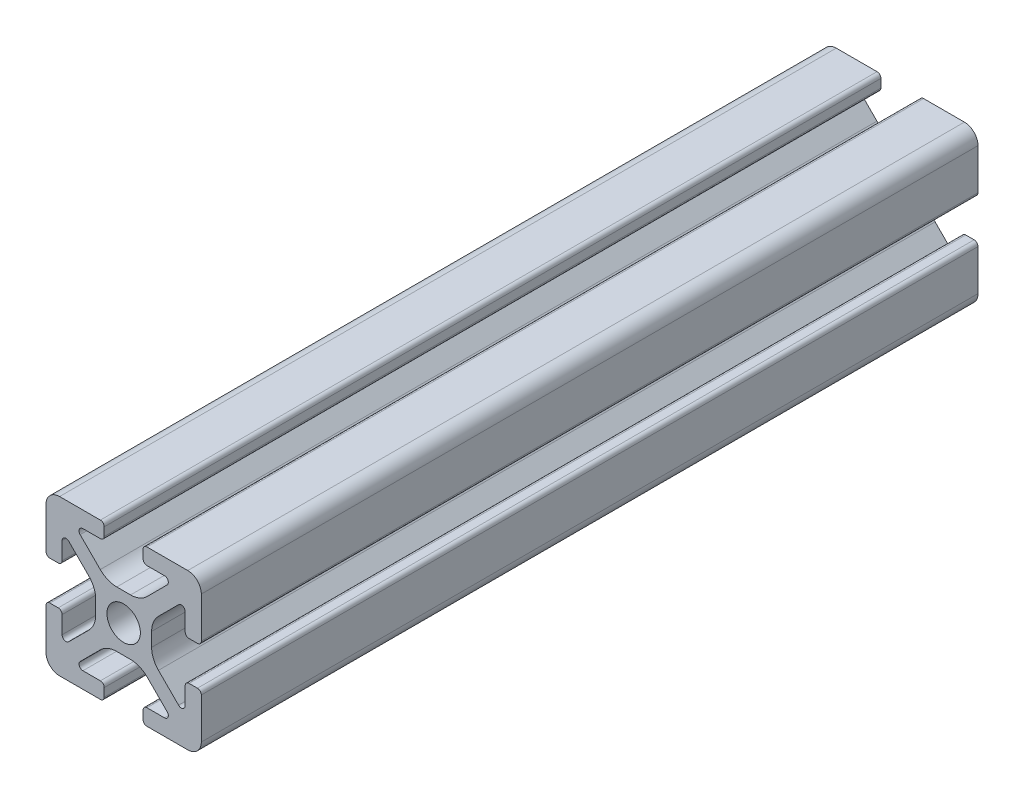
SolidWorks part; units mm, degrees
material "6061 Alloy"
ref_plane "Front Plane" through (0, 0, 0) normal (0, 0, 1) x (1, 0, 0)
ref_plane "Top Plane" through (0, 0, 0) normal (0, 1, 0) x (1, 0, 0)
ref_plane "Right Plane" through (0, 0, 0) normal (1, 0, 0) x (0, 0, -1)
sketch "Sketch2" plane through (0, 0, 0) normal (0, 0, 1) x (1, 0, 0)
  line L0 (0, 10) -> (0, -10) construction
  line L1 (-10, 0) -> (10, 0) construction
  line L2 (2.5, -10) -> (10, -10)
  line L3 (10, -10) -> (10, -2.5)
  line L4 (2.5, -10) -> (2.5, -7.9246)
  line L5 (2.5, -7.9246) -> (6.4571, -7.9246)
  line L6 (6.4571, -7.9246) -> (2.1325, -3.6)
  line L7 (0, 0) -> (10, -10) construction
  line L8 (10, -2.5) -> (7.9246, -2.5)
  line L9 (7.9246, -2.5) -> (7.9246, -6.4571)
  line L10 (7.9246, -6.4571) -> (3.6, -2.1325)
  line L11 (5.7623, -4.2948) -> (4.2948, -5.7623) construction
  circle A0 centre (0, 0) radius 2.15
  arc A1 (5.25, -7.9246) -> (5.6036, -7.0711) centre (5.25, -7.4246) ccw construction
  point P8 (0, -3.6)
  point P16 (5.0286, -5.0286)
  dimension "Center Hole Diameter" = 4.3
  dimension "D3" = 0.5
  dimension "Rail Height" = 20
  dimension "Rail Width" = 20
  dimension "T-Slot Width" = 5
  dimension "Slot Depth" = 6.4
  dimension "Slot Inner Width" = 11.5
sketch "Sketch3" plane through (0, 0, 0) normal (1, 0, 0) x (0, 0, -1)
  line L0 (-152.4, -10) -> (152.4, -10) construction
  line L1 (-127, 0) -> (127, 0) construction
  line L2 (0, 10) -> (0, -10) construction
  line L3 (0, 10) -> (0, -10) construction
  point P6 (-127, 0)
  point P8 (127, 0)
  dimension "Length" = 304.8
  dimension "D1" = 25.4
sketch "Sketch4" plane through (0, 0, 0) normal (0, 0, 1) x (1, 0, 0)
  line L0 (3, -10) -> (8.25, -10)
  line L1 (2.5, -10) -> (10, -10) construction
  line L2 (2.5, -10) -> (2.5, -7.9246) construction
  line L3 (2.5, -7.9246) -> (6.4571, -7.9246) construction
  line L4 (2.5, -8.4246) -> (2.5, -9.5)
  line L5 (3, -7.9246) -> (5.25, -7.9246)
  line L6 (0, -3.6) -> (0.8898, -3.6)
  line L7 (6.4571, -7.9246) -> (2.1325, -3.6) construction
  line L8 (3.0112, -4.4787) -> (5.6036, -7.0711)
  line L9 (10, -10) -> (10, -2.5) construction
  line L10 (7.9246, -6.4571) -> (3.6, -2.1325) construction
  line L11 (7.9246, -2.5) -> (7.9246, -6.4571) construction
  line L12 (7.9246, -5.25) -> (7.9246, -3)
  line L13 (10, -2.5) -> (7.9246, -2.5) construction
  line L14 (8.4246, -2.5) -> (9.5, -2.5)
  line L15 (10, -3) -> (10, -8.25)
  line L16 (7.0711, -5.6036) -> (4.4787, -3.0112)
  line L17 (3.6, 0) -> (3.6, -0.8898)
  line L18 (-10, 0) -> (10, 0) construction
  line L19 (0, -3.6) -> (0, -2.15)
  line L20 (0, 10) -> (0, -10) construction
  line L21 (3.6, 0) -> (2.15, 0)
  arc A0 (2.5, -9.5) -> (3, -10) centre (3, -9.5) ccw
  arc A1 (5.25, -7.9246) -> (5.6036, -7.0711) centre (5.25, -7.4246) ccw construction
  arc A2 (2.5, -8.4246) -> (3, -7.9246) centre (3, -8.4246) cw
  arc A3 (5.25, -7.9246) -> (5.6036, -7.0711) centre (5.25, -7.4246) ccw
  arc A4 (0.8898, -3.6) -> (3.0112, -4.4787) centre (0.8898, -6.6) cw
  arc A5 (8.25, -10) -> (10, -8.25) centre (8.25, -8.25) ccw
  arc A6 (7.0711, -5.6036) -> (7.9246, -5.25) centre (7.4246, -5.25) ccw
  arc A7 (7.9246, -3) -> (8.4246, -2.5) centre (8.4246, -3) cw
  arc A8 (9.5, -2.5) -> (10, -3) centre (9.5, -3) cw
  arc A9 (4.4787, -3.0112) -> (3.6, -0.8898) centre (6.6, -0.8898) cw
  circle A10 centre (0, 0) radius 2.15 construction
  arc A11 (0, -2.15) -> (2.15, 0) centre (0, 0) ccw
  dimension "D1" = 1.75
  dimension "D2" = 3
extrude "Boss-Extrude1" add sketch "Sketch4" along normal mid plane 100
mirror "Mirror1" about plane through (0, 0, 0) normal (1, 0, 0) of bodies 134
mirror "Mirror2" about plane through (0, 0, 0) normal (0, 1, 0) of bodies 135
equation "\"D3@Sketch2\"=\"T-Slot Width@Sketch2\"*0.1"
equation "\"D1@Sketch4\"=\"D3@Sketch2\"*3.5"
equation "\"D2@Sketch4\"=\"D3@Sketch2\"*6"
equation "\"D1@Boss-Extrude1\"=\"Length@Sketch3\""
